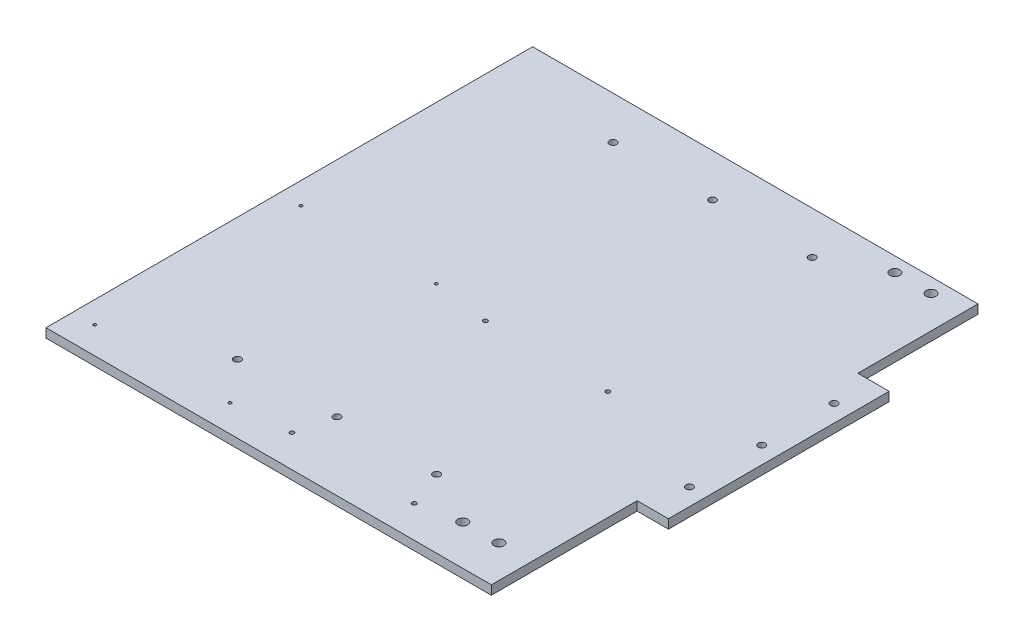
SolidWorks part; units mm, degrees
material "Cedar"
ref_plane "Front Plane" through (0, 0, 0) normal (0, 0, 1) x (1, 0, 0)
ref_plane "Top Plane" through (0, 0, 0) normal (0, 1, 0) x (1, 0, 0)
ref_plane "Right Plane" through (0, 0, 0) normal (1, 0, 0) x (0, 0, -1)
sketch "Sketch1" plane through (0, 0, 0) normal (0, 1, 0) x (1, 0, 0)
  line L0 (72.8376, -16.2766) -> (72.8376, -52.4668) construction
  line L1 (-156.5, -171) -> (156.5, -171)
  line L2 (-156.5, -171) -> (-156.5, 171)
  line L3 (-156.5, 171) -> (156.5, 171)
  line L4 (156.5, -171) -> (156.5, 171)
  line L5 (-156.5, -171) -> (156.5, 171) construction
  line L6 (-156.5, 171) -> (156.5, -171) construction
  point P0 (0, 0)
  dimension "D1" = 342
  dimension "D2" = 313
extrude "Boss-Extrude1" add sketch "Sketch1" against normal blind 6.35
ref_plane "Plane1" through (0, 0, -9) normal (0, 0, -1) x (-1, 0, 0)
sketch "Sketch3" plane through (0, 0, 0) normal (0, 1, 0) x (1, 0, 0)
  line L0 (156.5, 9) -> (-156.5, 9) construction
  line L1 (156.5, -171) -> (156.5, 171) construction
  line L2 (-156.5, 171) -> (-156.5, -171) construction
  line L3 (55, 9) -> (-55, 9) construction
  line L4 (156.5, 86.5702) -> (156.5, -68.5702)
  line L5 (156.5, -68.5702) -> (178.5, -68.5702)
  line L6 (178.5, -68.5702) -> (178.5, 86.5702)
  line L7 (178.5, 86.5702) -> (156.5, 86.5702)
  line L8 (166.5, 59.8) -> (166.5, 9) construction
  circle A0 centre (166.5, 9) radius 2.5
  circle A1 centre (166.5, -41.8) radius 2.5
  circle A2 centre (166.5, 59.8) radius 2.5
  point P10 (156.5, 9)
  dimension "D2" = 5
  dimension "D4" = 5
  dimension "D5" = 50.8
  dimension "D1" = 22
  dimension "D3" = 10
  dimension "D6" = 0
extrude "Boss-Extrude2" add sketch "Sketch3" against normal blind 6.35
sketch "Sketch2" plane through (0, 0, 0) normal (0, 1, 0) x (1, 0, 0)
  line L0 (156.5, 9) -> (-156.5, 9) construction
  line L1 (156.5, -171) -> (156.5, -68.5702) construction
  line L2 (-156.5, 171) -> (-156.5, -171) construction
  line L3 (0, -123) -> (0, -171) construction
  line L4 (55, 9) -> (-55, 9) construction
  line L5 (156.5, -123) -> (-156.5, -123) construction
  line L6 (-156.5, -171) -> (156.5, -171) construction
  circle A0 centre (0, -123) radius 2.5
  circle A1 centre (-70, -123) radius 2.5
  circle A2 centre (70, -123) radius 2.5
  circle A3 centre (-70, 141) radius 2.5
  circle A4 centre (0, 141) radius 2.5
  circle A5 centre (70, 141) radius 2.5
  dimension "D2" = 5
  dimension "D3" = 5
  dimension "D4" = 70
  dimension "D1" = 132
extrude "Cut-Extrude1" cut sketch "Sketch2" against normal through all
sketch "Sketch4" plane through (0, 0, 0) normal (0, 1, 0) x (1, 0, 0)
  line L0 (156.5, -171) -> (156.5, -68.5702) construction
  line L1 (108.24, -142.84) -> (133.64, -142.84) construction
  line L2 (-156.5, -171) -> (156.5, -171) construction
  circle A0 centre (133.64, -142.84) radius 3.5
  circle A1 centre (108.24, -142.84) radius 3.5
  dimension "D1" = 7
  dimension "D2" = 7
  dimension "D3" = 25.4
  dimension "D4" = 22.86
  dimension "D5" = 28.16
extrude "Cut-Extrude2" cut sketch "Sketch4" against normal through all
mirror "Mirror1" about plane through (0, 0, -9) normal (0, 0, -1) of "Cut-Extrude2"
sketch "Sketch5" plane through (0, 0, 0) normal (0, 1, 0) x (1, 0, 0)
  circle A29 centre (79.77, -148.4704) radius 1.5
  circle A30 centre (-6.23, -148.4704) radius 1.5
  circle A31 centre (-6.23, -12.4704) radius 1.5
  circle A32 centre (79.77, -12.4704) radius 1.5
  circle A33 centre (-46.1139, -7.1139) radius 1.05
  circle A34 centre (-46.1139, -152.1139) radius 1.05
  circle A35 centre (-141.1139, -7.1139) radius 1.05
  circle A36 centre (-141.1139, -152.1139) radius 1.05
  point P0 (0, 0)
extrude "Cut-Extrude3" cut sketch "Sketch5" against normal through all
